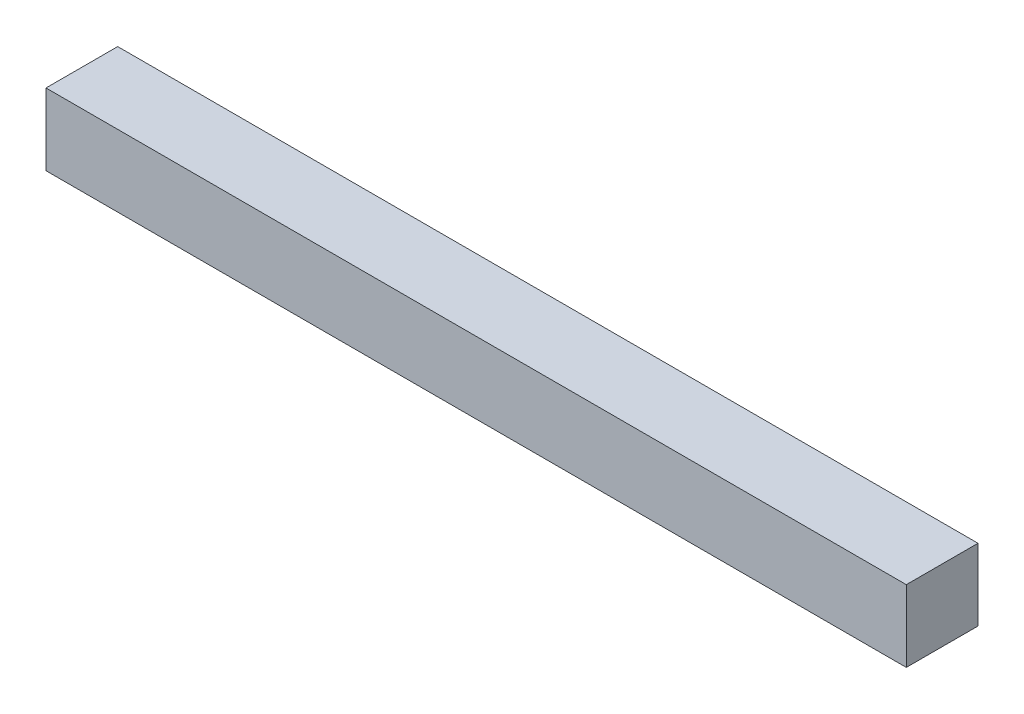
SolidWorks part; units mm, degrees
ref_plane "Front Plane" through (0, 0, 0) normal (0, 0, 1) x (1, 0, 0)
ref_plane "Top Plane" through (0, 0, 0) normal (0, 1, 0) x (1, 0, 0)
ref_plane "Right Plane" through (0, 0, 0) normal (1, 0, 0) x (0, 0, -1)
sketch "Sketch1" plane through (0, 0, 0) normal (1, 0, 0) x (0, 0, -1)
  line L1 (0, 0) -> (-25.4, 0)
  line L2 (0, 0) -> (0, 25.4)
  line L3 (0, 25.4) -> (-25.4, 25.4)
  line L4 (-25.4, 0) -> (-25.4, 25.4)
  dimension "D1" = 25.4
  dimension "D2" = 25.4
extrude "Boss-Extrude1" add sketch "Sketch1" along normal blind 304.8
